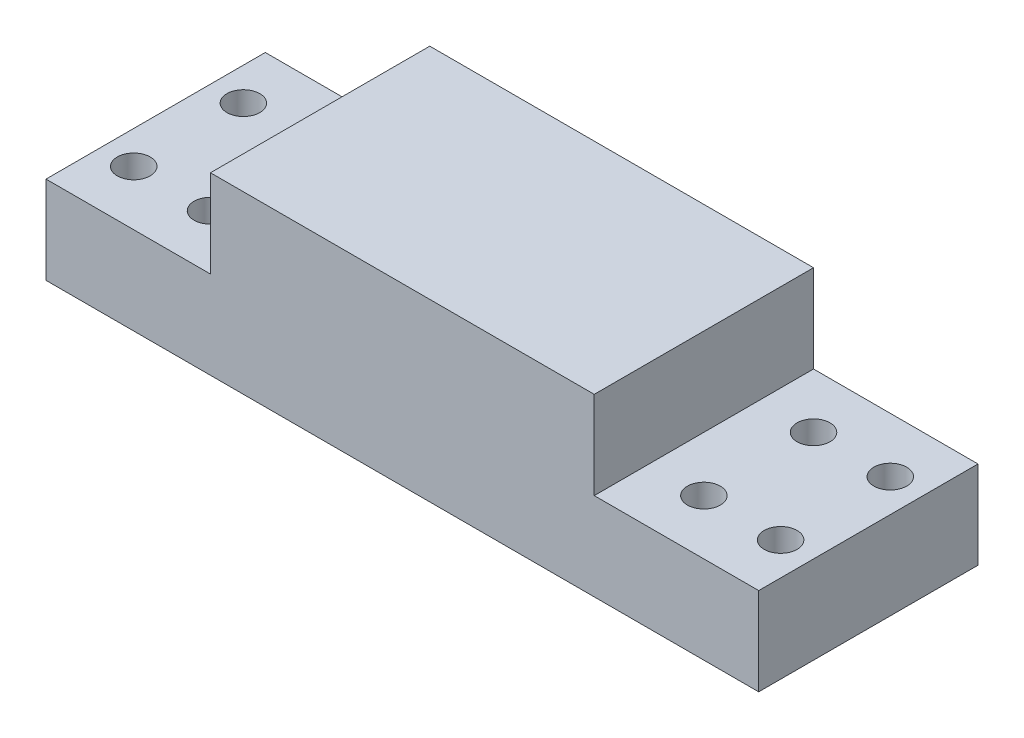
SolidWorks part; units mm, degrees
ref_plane "Front Plane" through (0, 0, 0) normal (0, 0, 1) x (1, 0, 0)
ref_plane "Top Plane" through (0, 0, 0) normal (0, 1, 0) x (1, 0, 0)
ref_plane "Right Plane" through (0, 0, 0) normal (1, 0, 0) x (0, 0, -1)
sketch "Sketch1" plane through (0, 0, 0) normal (0, 1, 0) x (1, 0, 0)
  line L0 (0, 0) -> (17.5, 0)
  line L1 (17.5, 0) -> (17.5, 10)
  line L2 (17.5, 10) -> (-17.5, 10)
  line L3 (-17.5, 10) -> (-17.5, 0)
  line L4 (-17.5, 0) -> (-17.5, -10)
  line L5 (-17.5, -10) -> (17.5, -10)
  line L6 (17.5, -10) -> (17.5, 0)
  line L7 (17.5, 10) -> (32.5, 10)
  line L8 (32.5, 10) -> (32.5, -10)
  line L9 (32.5, -10) -> (17.5, -10)
  line L10 (-17.5, 10) -> (-32.5, 10)
  line L11 (-32.5, 10) -> (-32.5, -10)
  line L12 (-32.5, -10) -> (-17.5, -10)
  line L13 (-32.5, 10) -> (-32.5, 0)
  line L14 (-17.5, 0) -> (-17.5, 5)
  line L15 (-17.5, 5) -> (-22.5, 5)
  line L16 (-22.5, 5) -> (-29.5, 5)
  line L17 (-29.5, 5) -> (-29.5, -5)
  line L18 (17.5, 0) -> (17.5, 5)
  line L19 (17.5, 0) -> (32.5, 0)
  line L20 (32.5, 0) -> (27.5, 0)
  line L21 (17.5, 5) -> (22.5, 5)
  line L22 (22.5, 5) -> (29.5, 5)
  line L23 (17.5, -5) -> (22.5, -5)
  line L24 (22.5, -5) -> (29.5, -5)
  line L25 (-29.5, -5) -> (-22.5, -5)
  circle A11 centre (22.5, 5) radius 1.5
  circle A12 centre (29.5, 5) radius 1.5
  circle A13 centre (22.5, -5) radius 1.5
  circle A14 centre (29.5, -5) radius 1.5
  circle A15 centre (-22.5, 5) radius 1.5
  circle A16 centre (-29.5, 5) radius 1.5
  circle A17 centre (-22.5, -5) radius 1.5
  circle A18 centre (-29.5, -5) radius 1.5
extrude "Boss-Extrude3" add sketch "Sketch1" along normal blind 8
sketch "Sketch4" plane through (0, 0, 0) normal (0, -1, 0) x (1, 0, 0)
  line L0 (17.5, -10) -> (-17.5, -10)
  line L1 (-17.5, -10) -> (-17.5, 10)
  line L2 (-17.5, 10) -> (17.5, 10)
  line L3 (17.5, 10) -> (17.5, -10)
extrude "Boss-Extrude4" add sketch "Sketch4" against normal blind 16
